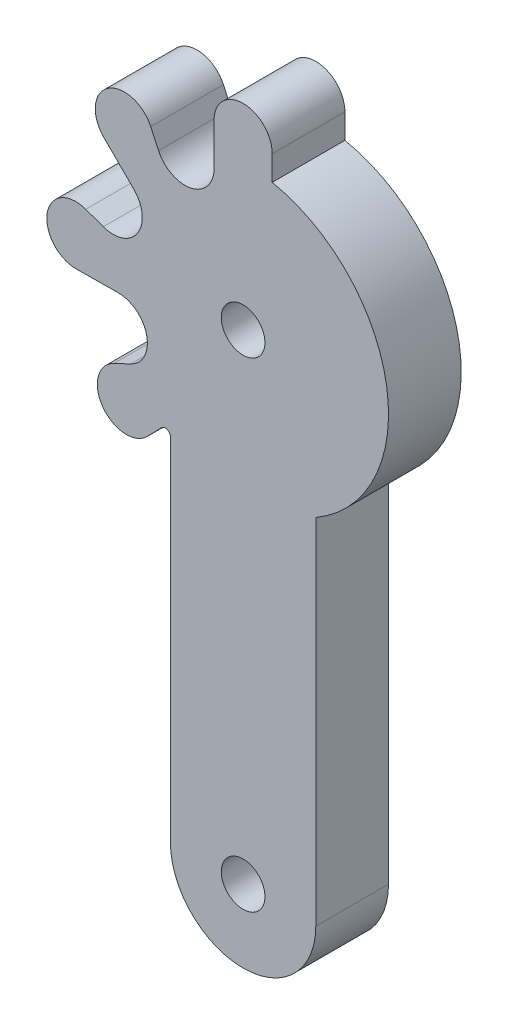
SolidWorks part; units mm, degrees
ref_plane "Front Plane" through (0, 0, 0) normal (0, 0, 1) x (1, 0, 0)
ref_plane "Top Plane" through (0, 0, 0) normal (0, 1, 0) x (1, 0, 0)
ref_plane "Right Plane" through (0, 0, 0) normal (1, 0, 0) x (0, 0, -1)
sketch "Sketch2" plane through (0, 0, 0) normal (0, 0, 1) x (1, 0, 0)
  line L0 (0, 0) -> (0, -33) construction
  line L1 (5, -8.6603) -> (5, -33)
  line L2 (-5, -8.8603) -> (-5, -33)
  line L3 (0, 0) -> (0, 27.439) construction
  line L5 (-2, 0) -> (-2, 0.0005)
  line L8 (-9.5743, 6.6771) -> (-7.527, 4.647)
  line L9 (-1.998, 8.6173) -> (-1.9973, 11.5)
  line L12 (-9.6145, 1.3458) -> (-10.8202, 1.7812)
  line L14 (-11.4996, -2.0999) -> (-8.6, -2.074)
  line L16 (-7.7245, -5.8807) -> (-8.8826, -6.4304)
  line L17 (-6.5923, -9.6328) -> (-5.6015, -8.6157)
  line L22 (-5.8123, 7.7761) -> (-6.3518, 8.939)
  line L23 (2.0023, 9.7975) -> (2.0027, 11.5)
  arc A1 (-5, -33) -> (5, -33) centre (0, -33) ccw
  arc A2 (5, -8.6603) -> (2.0023, 9.7975) centre (0, 0) ccw
  circle A3 centre (0, -33) radius 1.5
  circle A4 centre (0, 0) radius 13.5 construction
  circle A5 centre (0, 0) radius 7.5 construction
  arc A15 (2.0027, 11.4995) -> (-1.9973, 11.5) centre (0.0027, 11.5) ccw
  circle A16 centre (0, 0) radius 2 construction
  arc A17 (-5.8123, 7.7761) -> (-1.998, 8.6173) centre (-3.998, 8.6178) ccw
  arc A18 (-6.3518, 8.939) -> (-9.5743, 6.6771) centre (-8.166, 8.0973) ccw
  arc A19 (-9.6145, 1.3458) -> (-7.527, 4.647) centre (-8.9352, 3.2269) ccw
  arc A20 (-10.8202, 1.7812) -> (-11.4638, -2.0996) centre (-11.4996, -0.0999) ccw
  arc A21 (-7.7245, -5.8807) -> (-8.6, -2.074) centre (-8.5822, -4.0739) ccw
  arc A22 (-8.8826, -6.4304) -> (-6.5923, -9.6328) centre (-8.0249, -8.2372) ccw
  arc A23 (-5, -8.8603) -> (-5.6015, -8.6157) centre (-5.3505, -8.8603) ccw
  circle A24 centre (0, 0) radius 1.5
  arc A25 (-8.0078, -5.9896) -> (-7.9937, -6.0084) centre (0, 0) ccw
  point P3 (0, -16.5)
  point P18 (-8.3035, -6.1555)
  point P23 (-8.5506, 5.6621)
  point P28 (-6.082, 8.3575)
  dimension "D1" = 5
  dimension "D2" = 20
  dimension "D8" = 3
  dimension "D9" = 27
  dimension "D10" = 15
  dimension "D11" = 4
  dimension "D12" = 4
  dimension "D13" = 4
  dimension "D14" = 4
  dimension "D15" = 4
  dimension "D16" = 4
  dimension "D17" = 4
  dimension "D18" = 4
  dimension "D29" = 3
  dimension "D3" = 24.3397
  dimension "D4" = 33
  dimension "D5" = 5
  dimension "D6" = 5
  dimension "D7" = 8.8603
  dimension "D19" = 8.2372
  dimension "D20" = 4.0739
  dimension "D21" = 6.1555
  dimension "D22" = 1.9971
  dimension "D23" = 5.6621
  dimension "D24" = 2
  dimension "D25" = 8.3575
  dimension "D26" = 8.6178
  dimension "D27" = 2
  dimension "D28" = 2
extrude "Boss-Extrude1" add sketch "Sketch2" along normal blind 5
